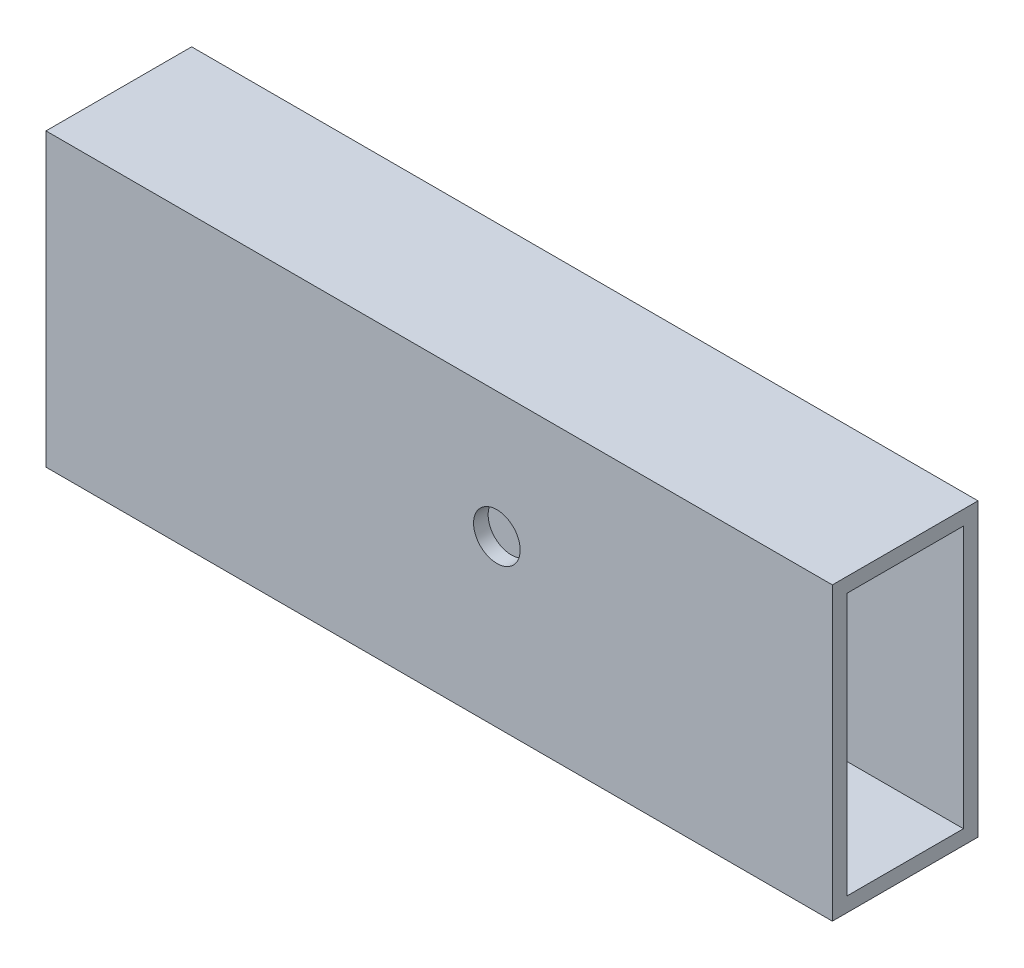
SolidWorks part; units mm, degrees
ref_plane "Front Plane" through (0, 0, 0) normal (0, 0, 1) x (1, 0, 0)
ref_plane "Top Plane" through (0, 0, 0) normal (0, 1, 0) x (1, 0, 0)
ref_plane "Right Plane" through (0, 0, 0) normal (1, 0, 0) x (0, 0, -1)
sketch "Sketch5" plane through (0, 0, 0) normal (1, 0, 0) x (0, 0, -1)
  line L1 (12.5, -25) -> (-12.5, -25)
  line L2 (12.5, -25) -> (12.5, 25)
  line L3 (12.5, 25) -> (-12.5, 25)
  line L4 (-12.5, -25) -> (-12.5, 25)
  line L5 (12.5, -25) -> (-12.5, 25) construction
  line L6 (12.5, 25) -> (-12.5, -25) construction
  point P0 (0, 0)
extrude "Boss-Extrude2" add sketch "Sketch5" against normal blind 135
sketch "Sketch6" plane through (0, 0, 0) normal (1, 0, 0) x (0, 0, -1)
  line L1 (10, -22.5) -> (-10, -22.5)
  line L2 (10, -22.5) -> (10, 22.5)
  line L3 (10, 22.5) -> (-10, 22.5)
  line L4 (-10, -22.5) -> (-10, 22.5)
  line L5 (10, -22.5) -> (-10, 22.5) construction
  line L6 (10, 22.5) -> (-10, -22.5) construction
  point P0 (0, 0)
extrude "Cut-Extrude1" cut sketch "Sketch6" against normal blind 135
sketch "Sketch7" plane through (0, 0, 0) normal (0, 0, 1) x (1, 0, 0)
  circle A0 centre (-57.6003, 3.3891) radius 4
extrude "Cut-Extrude4" cut sketch "Sketch7" along normal through all
